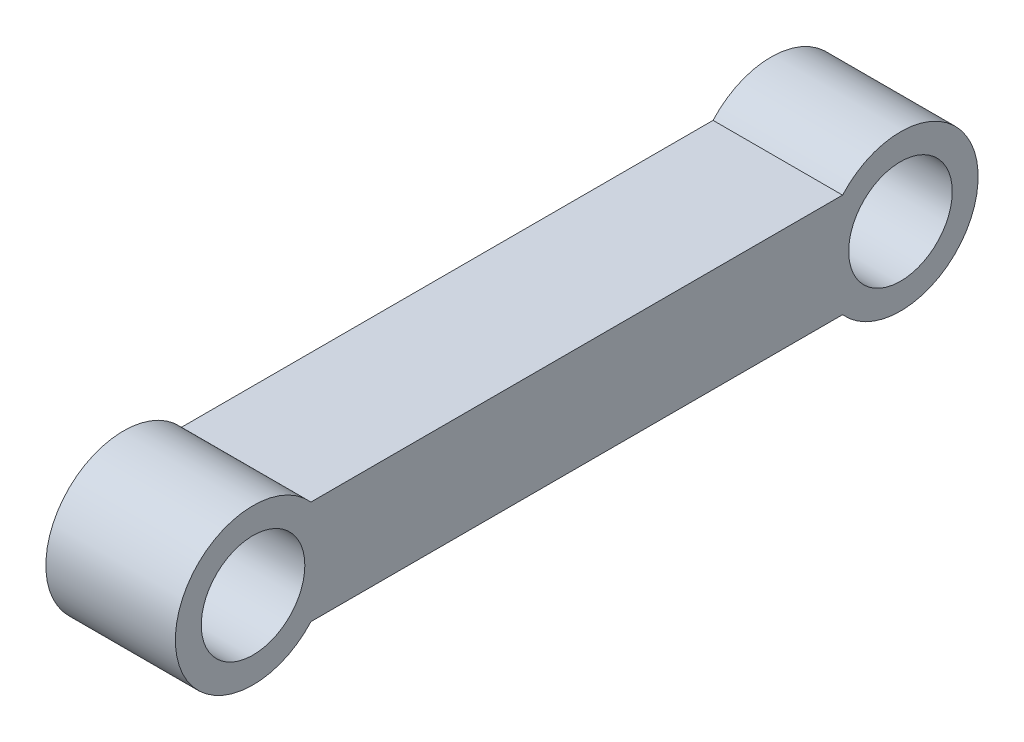
SolidWorks part; units mm, degrees
material "Thornel Mat VMA"
ref_plane "Front Plane" through (0, 0, 0) normal (0, 0, 1) x (1, 0, 0)
ref_plane "Top Plane" through (0, 0, 0) normal (0, 1, 0) x (1, 0, 0)
ref_plane "Right Plane" through (0, 0, 0) normal (1, 0, 0) x (0, 0, -1)
sketch "LinkFrame" plane through (0, 0, 0) normal (1, 0, 0) x (0, 0, -1)
  line L0 (-240.3455, -226.2633) -> (259.6545, -226.2633) construction
  line L1 (-195.6242, -186.2633) -> (214.9331, -186.2633)
  line L2 (-195.6242, -266.2633) -> (214.9331, -266.2633)
  arc A1 (214.9331, -266.2633) -> (214.9331, -186.2633) centre (259.6545, -226.2633) ccw
  arc A2 (-195.6242, -186.2633) -> (-195.6242, -266.2633) centre (-240.3455, -226.2633) ccw
  circle A5 centre (-240.3455, -226.2633) radius 40
  circle A6 centre (259.6545, -226.2633) radius 40
  dimension "D1" = 120
  dimension "D2" = 120
  dimension "D5" = 80
  dimension "D6" = 80
  dimension "D3" = 500
  dimension "D4" = 80
  dimension "D7" = 44.7214
  dimension "D8" = 44.7214
extrude "Boss-Extrude1" add sketch "LinkFrame" along normal blind 100
equation "\"D1@LinkFrame\" = 1.5 * \"HoleMountDiameter@PrintingPress.Assembly\""
equation "\"D2@LinkFrame\" = 1.5 * \"HoleMountDiameter@PrintingPress.Assembly\""
equation "\"LinkLength\"= 50cm"
equation "\"D3@LinkFrame\" = \"LinkLength\""
equation "\"D4@LinkFrame\" = \"HoleMountDiameter@PrintingPress.Assembly\""
equation "\"D5@LinkFrame\"=\"HoleMountDiameter@PrintingPress.Assembly\""
equation "\"D6@LinkFrame\"=\"HoleMountDiameter@PrintingPress.Assembly\""
equation "\"D1@Boss-Extrude1\"=\"RivetLength@PrintingPress.Assembly\""
